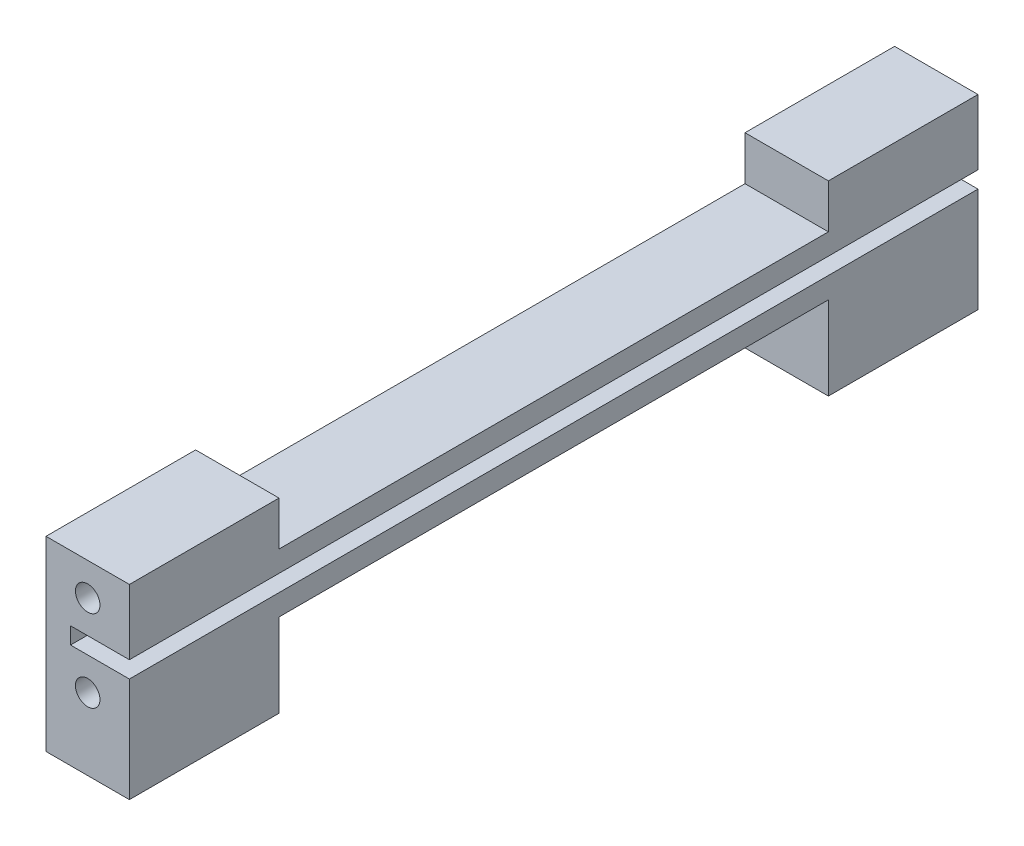
SolidWorks part; units mm, degrees
ref_plane "Front Plane" through (0, 0, 0) normal (0, 0, 1) x (1, 0, 0)
ref_plane "Top Plane" through (0, 0, 0) normal (0, 1, 0) x (1, 0, 0)
ref_plane "Right Plane" through (0, 0, 0) normal (1, 0, 0) x (0, 0, -1)
sketch "Sketch5" plane through (0, 0, 0) normal (1, 0, 0) x (0, 0, -1)
  line L0 (0, 0) -> (15.25, 0)
  line L1 (15.25, 0) -> (15.25, 4.5)
  line L2 (15.25, 4.5) -> (71.25, 4.5)
  line L3 (71.25, 4.5) -> (71.25, 0)
  line L4 (71.25, 0) -> (86.5, 0)
  line L5 (86.5, 0) -> (86.5, 15)
  line L6 (86.5, 15) -> (71.25, 15)
  line L7 (71.25, 15) -> (71.25, 10.5)
  line L8 (71.25, 10.5) -> (15.25, 10.5)
  line L9 (15.25, 10.5) -> (15.25, 15)
  line L10 (15.25, 15) -> (0, 15)
  line L11 (0, 15) -> (0, 0)
  dimension "D1" = 15.25
  dimension "D2" = 15.25
  dimension "D3" = 56
  dimension "D4" = 4.5
  dimension "D5" = 56
  dimension "D6" = 4.5
  dimension "D7" = 4.5
  dimension "D8" = 15
  dimension "D9" = 15.25
extrude "Boss-Extrude2" add sketch "Sketch5" along normal blind 8.5 contours L8 L9 L10 L11 L0 L1 L2 L3 L4 L5 L6 L7
sketch "Sketch6" plane through (0, 0, 0) normal (0, 0, 1) x (1, 0, 0)
  line L0 (8.5, 0) -> (8.5, 6.65)
  line L1 (8.5, 15) -> (8.5, 0) construction
  line L2 (8.5, 6.65) -> (2.5, 6.65)
  line L3 (2.5, 6.65) -> (2.5, 8.35)
  line L4 (2.5, 8.35) -> (8.5, 8.35)
  line L5 (8.5, 8.35) -> (8.5, 6.65)
  dimension "D1" = 6.65
  dimension "D2" = 6
  dimension "D3" = 1.7
extrude "Cut-Extrude3" cut sketch "Sketch6" against normal through all contours L2 L3 L4 L5
sketch "Sketch8" plane through (0, 0, 0) normal (0, 0, 1) x (1, 0, 0)
  line L0 (0, 0) -> (4.25, 0)
  line L1 (8.5, 0) -> (0, 0) construction
  line L2 (4.25, 0) -> (4.25, 3.325)
  line L3 (4.25, 15) -> (4.25, 11.675)
  line L4 (8.5, 15) -> (0, 15) construction
  dimension "D1" = 3.325
  dimension "D2" = 3.325
hole_wizard "M3x0.5 Tapped Hole4" positions "Sketch17" profile "Sketch18" tap size "M3x0.5" standard "ANSI Metric"
sketch "Sketch17" plane through (0, 0, 0) normal (0, 0, 1) x (1, 0, 0)
  point P0 (4.25, 3.325)
  point P4 (4.25, 11.675)
sketch "Sketch18" plane through (4.25, 3.325, 0) normal (1, 0, 0) x (0, -1, 0)
  line L0 (0, 0) -> (0, 6.7511)
  line L1 (0, 6.7511) -> (1.25, 6)
  line L2 (1.25, 6) -> (1.25, 0)
  line L5 (1.25, 0) -> (0, 0)
  line L10 (0, 6.7511) -> (-1.25, 6) construction
  line L11 (0, -6.35) -> (0, 107.95) construction
  dimension "Tap Drill Dia." = 2.5
  dimension "Tap Drill Depth" = 6
  dimension "Drill Angle" = 118
ref_plane "Plane1" through (0, 0, -43.25) normal (0, 0, -1) x (-1, 0, 0)
sketch "Sketch19" plane through (0, 0, 0) normal (0, 0, 1) x (1, 0, 0)
  line L0 (2.5, 7.5) -> (0, 7.5)
  line L1 (2.5, 6.65) -> (2.5, 8.35) construction
  line L2 (0, 15) -> (0, 0) construction
ref_plane "Plane2" through (0, 7.5, 0) normal (0, -1, 0) x (-1, 0, 0)
mirror "Mirror3" about plane through (0, 0, -43.25) normal (0, 0, -1) of "M3x0.5 Tapped Hole4"
sketch "Sketch20" plane through (0, 0, 0) normal (0, -1, 0) x (1, 0, 0)
  line L1 (0, 0) -> (8.5, 0)
  line L2 (0, 0) -> (0, -15.25)
  line L3 (0, -15.25) -> (8.5, -15.25)
  line L4 (8.5, 0) -> (8.5, -15.25)
extrude "Boss-Extrude3" add sketch "Sketch20" along normal blind 4
sketch "Sketch23" plane through (0, 0, 0) normal (0, -1, 0) x (1, 0, 0)
  line L1 (0, -86.5) -> (8.5, -86.5)
  line L2 (0, -86.5) -> (0, -71.25)
  line L3 (0, -71.25) -> (8.5, -71.25)
  line L4 (8.5, -86.5) -> (8.5, -71.25)
extrude "Boss-Extrude4" add sketch "Sketch23" along normal blind 4
